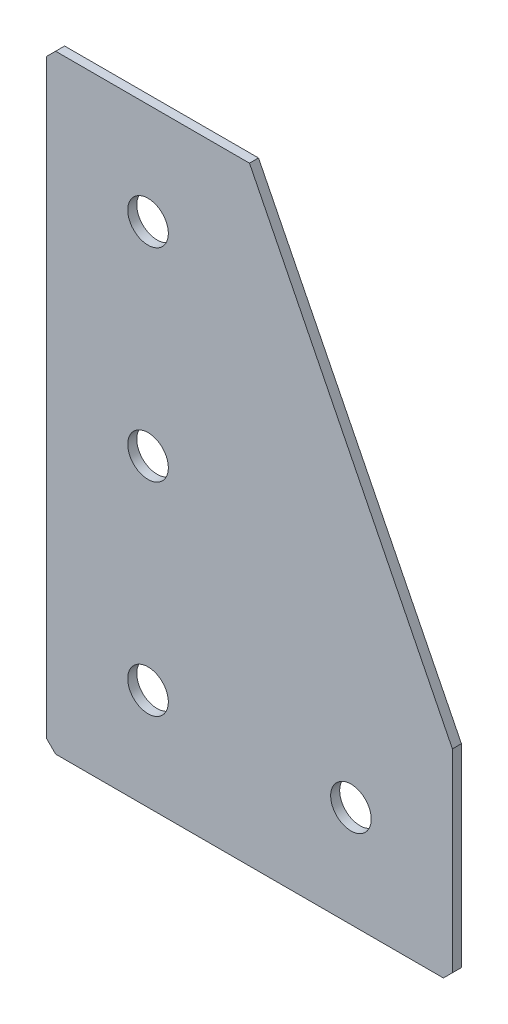
SolidWorks part; units mm, degrees
material "Простая углеродистая сталь"
ref_plane "Спереди(Плоскость XY)" through (0, 0, 0) normal (0, 0, 1) x (1, 0, 0)
ref_plane "Сверху(Плоскость XZ)" through (0, 0, 0) normal (0, 1, 0) x (1, 0, 0)
ref_plane "Справа(Плоскость ZY)" through (0, 0, 0) normal (1, 0, 0) x (0, 0, -1)
sketch "Эскиз1" plane through (0, 0, 0) normal (0, 0, -1) x (1, 0, 0)
  line L0 (0, 0) -> (0, 135)
  line L1 (0, 135) -> (90, 135)
  line L2 (90, 135) -> (90, 90)
  line L3 (90, 90) -> (45, 90) construction
  line L4 (45, 90) -> (45, 0) construction
  line L5 (45, 0) -> (0, 0)
  line L6 (90, 90) -> (45, 0)
  dimension "D1" = 135
  dimension "D3" = 45
extrude "Бобышка-Вытянуть1" add sketch "Эскиз1" along normal blind 2
hole_wizard "Отверстие с зазором M81" positions "Эскиз2" profile "Эскиз3" hole size "M8" standard "DIN" end condition through all
sketch "Эскиз2" plane through (0, 0, -2) normal (0, 0, -1) x (1, 0, 0)
  line L1 (0, 0) -> (45, 0) construction
  line L7 (22.5, 0) -> (22.5, 22.5) construction
  line L10 (0, 135) -> (0, 0) construction
  point P0 (67.5, 112.5)
  point P2 (22.5, 112.5)
  point P4 (22.5, 67.5)
  point P6 (22.5, 22.5)
  dimension "D1" = 45
  dimension "D2" = 45
  dimension "D3" = 45
  dimension "D4" = 22.5
  dimension "D5" = 22.5
sketch "Эскиз3" plane through (67.5, -112.5, -2) normal (1, 0, 0) x (0, 1, 0)
  line L0 (0, 0) -> (0, 2)
  line L1 (0, 2) -> (4.5, 2)
  line L2 (4.5, 2) -> (4.5, 0)
  line L5 (4.5, 0) -> (0, 0)
  line L11 (0, -6.35) -> (0, 107.95) construction
  dimension "Диаметр сквозного отверстия" = 9
  dimension "Глубина сквозного отверстия" = 2
chamfer "Фаска1" distance 2 angle 45 3 edges at (0, 0, -1) (90, -135, -1) (0, -135, -1)
